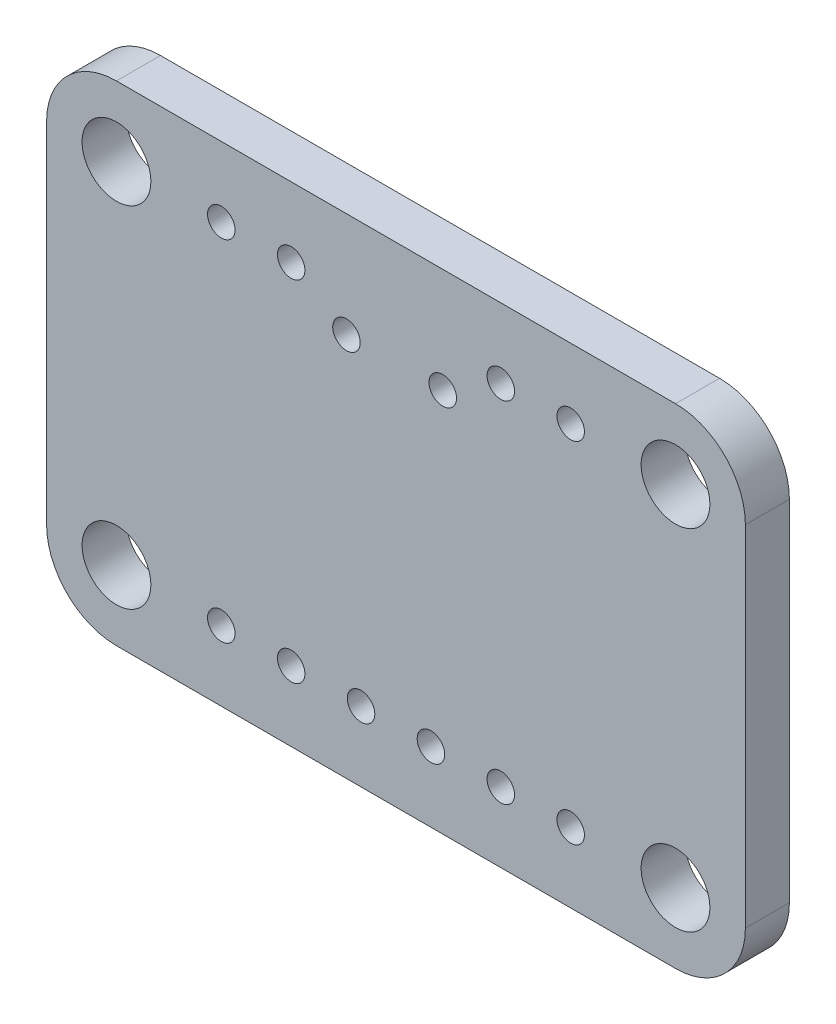
SolidWorks part; units mm, degrees
ref_plane "Front Plane" through (0, 0, 0) normal (0, 0, 1) x (1, 0, 0)
ref_plane "Top Plane" through (0, 0, 0) normal (0, 1, 0) x (1, 0, 0)
ref_plane "Right Plane" through (0, 0, 0) normal (1, 0, 0) x (0, 0, -1)
sketch "Model" plane through (0, 0, 0) normal (0, 0, 1) x (1, 0, 0)
  line L0 (0, 15.24) -> (0, 2.54)
  line L1 (2.54, 0) -> (22.86, 0)
  line L2 (25.4, 2.54) -> (25.4, 15.24)
  line L3 (22.86, 17.78) -> (2.54, 17.78)
  line L4 (15.6085, 7.087) -> (15.6085, 6.375)
  line L5 (14.7575, 7.087) -> (14.7575, 6.375)
  line L6 (15.5765, 6.731) -> (14.7765, 6.731)
  line L7 (7.1505, 9.652) -> (7.1505, 10.414)
  line L8 (8.4705, 9.677) -> (8.4705, 10.414)
  line L9 (7.3025, 10.033) -> (8.3185, 10.033)
  line L10 (8.2425, 6.7695) -> (8.2425, 6.0575)
  line L11 (7.3915, 6.7695) -> (7.3915, 6.0575)
  line L12 (8.2105, 6.4135) -> (7.4105, 6.4135)
  line L13 (24.819, 5.89) -> (20.569, 5.89)
  line L14 (20.569, 5.89) -> (20.569, 11.99)
  line L15 (20.569, 11.99) -> (24.819, 11.99)
  line L16 (24.819, 11.99) -> (24.819, 5.89)
  line L17 (23.119, 5.89) -> (20.519, 5.89)
  line L18 (20.519, 5.89) -> (20.519, 6.99)
  line L19 (20.519, 10.79) -> (20.519, 11.99)
  line L20 (20.519, 11.99) -> (23.119, 11.99)
  line L21 (24.819, 6.79) -> (24.819, 10.99)
  line L22 (0.6445, 11.89) -> (4.8945, 11.89)
  line L23 (4.8945, 11.89) -> (4.8945, 5.79)
  line L24 (4.8945, 5.79) -> (0.6445, 5.79)
  line L25 (0.6445, 5.79) -> (0.6445, 11.89)
  line L26 (2.3445, 11.89) -> (4.9445, 11.89)
  line L27 (4.9445, 11.89) -> (4.9445, 10.79)
  line L28 (4.9445, 6.99) -> (4.9445, 5.79)
  line L29 (4.9445, 5.79) -> (2.3445, 5.79)
  line L30 (0.6445, 10.99) -> (0.6445, 6.79)
  line L31 (3.6703, 12.5095) -> (3.9878, 12.2555)
  line L32 (3.9878, 12.2555) -> (3.9878, 12.7635)
  line L33 (3.9878, 12.7635) -> (3.6703, 12.5095)
  line L34 (3.8767, 12.3444) -> (3.9878, 12.3444)
  line L35 (3.6862, 12.4968) -> (3.9878, 12.4968)
  line L36 (3.8449, 12.6492) -> (3.9878, 12.6492)
  line L37 (3.435, 12.1095) -> (4.16, 12.1095)
  line L38 (3.46, 12.9095) -> (4.16, 12.9095)
  line L39 (13.084, 8.258) -> (13.084, 5.458)
  line L40 (13.084, 5.458) -> (10.284, 5.458)
  line L41 (10.284, 5.458) -> (10.284, 8.258)
  line L42 (10.284, 8.258) -> (13.084, 8.258)
  line L43 (11.184, 7.658) -> (10.584, 7.658)
  line L44 (5.08, 3.175) -> (5.08, 1.905)
  line L45 (15.24, 15.875) -> (15.24, 14.605)
  line L46 (5.08, 15.875) -> (5.08, 14.605)
  line L47 (17.0435, 7.671) -> (17.0435, 10.871)
  line L48 (17.0435, 10.871) -> (18.6435, 10.871)
  line L49 (18.6435, 10.871) -> (18.6435, 7.671)
  line L50 (18.6435, 7.671) -> (17.0435, 7.671)
  line L51 (16.4435, 11.171) -> (19.2435, 11.171)
  line L52 (19.2435, 7.371) -> (16.4435, 7.371)
  line L53 (6.274, 12.802) -> (6.274, 12.09)
  line L54 (5.423, 12.802) -> (5.423, 12.09)
  line L55 (6.242, 12.446) -> (5.442, 12.446)
  line L56 (17.6053, 13.335) -> (16.8116, 13.335)
  line L57 (17.2085, 13.7318) -> (17.2085, 12.9382)
  line L58 (8.4613, 13.3985) -> (7.6676, 13.3985)
  line L59 (16.1, 10.57) -> (16.1, 16.17)
  line L60 (16.1, 16.17) -> (16.1, 17.57)
  line L61 (16.1, 17.57) -> (9.1, 17.57)
  line L62 (9.1, 17.57) -> (9.1, 16.17)
  line L63 (9.1, 16.17) -> (9.1, 10.57)
  line L64 (9.1, 10.57) -> (16.1, 10.57)
  line L65 (16.1, 16.17) -> (9.1, 16.17)
  arc A0 (0, 2.54) -> (2.54, 0) centre (2.54, 2.54) ccw
  arc A1 (22.86, 0) -> (25.4, 2.54) centre (22.86, 2.54) ccw
  arc A2 (25.4, 15.24) -> (22.86, 17.78) centre (22.86, 15.24) ccw
  arc A3 (2.54, 17.78) -> (0, 15.24) centre (2.54, 15.24) ccw
  circle A4 centre (6.35, 2.54) radius 0.5
  circle A5 centre (8.89, 2.54) radius 0.5
  circle A6 centre (11.43, 2.54) radius 0.5
  circle A7 centre (13.97, 2.54) radius 0.5
  circle A8 centre (16.51, 2.54) radius 0.5
  circle A9 centre (19.05, 2.54) radius 0.5
  circle A10 centre (16.51, 15.24) radius 0.5
  circle A11 centre (19.05, 15.24) radius 0.5
  circle A12 centre (6.35, 15.24) radius 0.5
  circle A13 centre (8.89, 15.24) radius 0.5
  circle A14 centre (2.54, 15.24) radius 1.25
  circle A15 centre (22.86, 15.24) radius 1.25
  circle A16 centre (2.54, 2.54) radius 1.25
  circle A17 centre (22.86, 2.54) radius 1.25
  circle A18 centre (10.9, 13.97) radius 0.5
  circle A19 centre (14.4, 13.97) radius 0.5
  circle A20 centre (7.366, 4.318) radius 0.2413
  circle A21 centre (1.3335, 10.0965) radius 0.2413
  circle A22 centre (1.397, 7.4295) radius 0.2413
  circle A23 centre (24.13, 10.0965) radius 0.2413
  circle A24 centre (24.003, 7.5565) radius 0.2413
  circle A25 centre (9.398, 10.3505) radius 0.2413
  circle A26 centre (7.112, 13.2715) radius 0.2413
  circle A27 centre (16.002, 4.6355) radius 0.2413
  circle A28 centre (21.7805, 10.4775) radius 0.2413
  circle A29 centre (3.7465, 7.366) radius 0.2413
  circle A30 centre (12.5948, 6.0742) radius 0.2413
  circle A31 centre (21.8059, 9.1901) radius 0.2413
  circle A32 centre (3.7465, 6.2738) radius 0.2413
  circle A33 centre (11.5126, 6.3056) radius 0.2413
  circle A34 centre (22.606, 8.0645) radius 0.2413
  circle A35 centre (18.8595, 12.065) radius 0.2413
  circle A36 centre (3.2385, 10.795) radius 0.2413
  arc A37 (15.5831, 6.375) -> (15.6339, 6.375) centre (15.6085, 6.375) ccw
  arc A38 (15.6339, 7.087) -> (15.5831, 7.087) centre (15.6085, 7.087) ccw
  arc A39 (14.7321, 6.375) -> (14.7829, 6.375) centre (14.7575, 6.375) ccw
  arc A40 (14.7829, 7.087) -> (14.7321, 7.087) centre (14.7575, 7.087) ccw
  arc A41 (14.7765, 6.8072) -> (14.7765, 6.6548) centre (14.7765, 6.731) ccw
  arc A42 (15.5765, 6.6548) -> (15.5765, 6.8072) centre (15.5765, 6.731) ccw
  arc A43 (7.1759, 10.414) -> (7.1251, 10.414) centre (7.1505, 10.414) ccw
  arc A44 (7.1251, 9.652) -> (7.1759, 9.652) centre (7.1505, 9.652) ccw
  arc A45 (8.4959, 10.414) -> (8.4451, 10.414) centre (8.4705, 10.414) ccw
  arc A46 (8.4451, 9.677) -> (8.4959, 9.677) centre (8.4705, 9.677) ccw
  arc A47 (8.3185, 9.9568) -> (8.3185, 10.1092) centre (8.3185, 10.033) ccw
  arc A48 (7.3025, 10.1092) -> (7.3025, 9.9568) centre (7.3025, 10.033) ccw
  arc A49 (8.2171, 6.0575) -> (8.2679, 6.0575) centre (8.2425, 6.0575) ccw
  arc A50 (8.2679, 6.7695) -> (8.2171, 6.7695) centre (8.2425, 6.7695) ccw
  arc A51 (7.3661, 6.0575) -> (7.4169, 6.0575) centre (7.3915, 6.0575) ccw
  arc A52 (7.4169, 6.7695) -> (7.3661, 6.7695) centre (7.3915, 6.7695) ccw
  arc A53 (7.4105, 6.4897) -> (7.4105, 6.3373) centre (7.4105, 6.4135) ccw
  arc A54 (8.2105, 6.3373) -> (8.2105, 6.4897) centre (8.2105, 6.4135) ccw
  arc A55 (20.569, 5.9281) -> (20.569, 5.8519) centre (20.569, 5.89) ccw
  arc A56 (24.819, 5.8519) -> (24.819, 5.9281) centre (24.819, 5.89) ccw
  arc A57 (20.6071, 11.99) -> (20.5309, 11.99) centre (20.569, 11.99) ccw
  arc A58 (20.5309, 5.89) -> (20.6071, 5.89) centre (20.569, 5.89) ccw
  arc A59 (24.819, 11.9519) -> (24.819, 12.0281) centre (24.819, 11.99) ccw
  arc A60 (20.569, 12.0281) -> (20.569, 11.9519) centre (20.569, 11.99) ccw
  arc A61 (24.7809, 5.89) -> (24.8571, 5.89) centre (24.819, 5.89) ccw
  arc A62 (24.8571, 11.99) -> (24.7809, 11.99) centre (24.819, 11.99) ccw
  arc A63 (20.519, 5.9281) -> (20.519, 5.8519) centre (20.519, 5.89) ccw
  arc A64 (23.119, 5.8519) -> (23.119, 5.9281) centre (23.119, 5.89) ccw
  arc A65 (20.5571, 6.99) -> (20.4809, 6.99) centre (20.519, 6.99) ccw
  arc A66 (20.4809, 5.89) -> (20.5571, 5.89) centre (20.519, 5.89) ccw
  arc A67 (20.5571, 11.99) -> (20.4809, 11.99) centre (20.519, 11.99) ccw
  arc A68 (20.4809, 10.79) -> (20.5571, 10.79) centre (20.519, 10.79) ccw
  arc A69 (23.119, 11.9519) -> (23.119, 12.0281) centre (23.119, 11.99) ccw
  arc A70 (20.519, 12.0281) -> (20.519, 11.9519) centre (20.519, 11.99) ccw
  arc A71 (24.8571, 10.99) -> (24.7809, 10.99) centre (24.819, 10.99) ccw
  arc A72 (24.7809, 6.79) -> (24.8571, 6.79) centre (24.819, 6.79) ccw
  arc A73 (4.8945, 11.8519) -> (4.8945, 11.9281) centre (4.8945, 11.89) ccw
  arc A74 (0.6445, 11.9281) -> (0.6445, 11.8519) centre (0.6445, 11.89) ccw
  arc A75 (4.8564, 5.79) -> (4.9326, 5.79) centre (4.8945, 5.79) ccw
  arc A76 (4.9326, 11.89) -> (4.8564, 11.89) centre (4.8945, 11.89) ccw
  arc A77 (0.6445, 5.8281) -> (0.6445, 5.7519) centre (0.6445, 5.79) ccw
  arc A78 (4.8945, 5.7519) -> (4.8945, 5.8281) centre (4.8945, 5.79) ccw
  arc A79 (0.6826, 11.89) -> (0.6064, 11.89) centre (0.6445, 11.89) ccw
  arc A80 (0.6064, 5.79) -> (0.6826, 5.79) centre (0.6445, 5.79) ccw
  arc A81 (4.9445, 11.8519) -> (4.9445, 11.9281) centre (4.9445, 11.89) ccw
  arc A82 (2.3445, 11.9281) -> (2.3445, 11.8519) centre (2.3445, 11.89) ccw
  arc A83 (4.9064, 10.79) -> (4.9826, 10.79) centre (4.9445, 10.79) ccw
  arc A84 (4.9826, 11.89) -> (4.9064, 11.89) centre (4.9445, 11.89) ccw
  arc A85 (4.9064, 5.79) -> (4.9826, 5.79) centre (4.9445, 5.79) ccw
  arc A86 (4.9826, 6.99) -> (4.9064, 6.99) centre (4.9445, 6.99) ccw
  arc A87 (2.3445, 5.8281) -> (2.3445, 5.7519) centre (2.3445, 5.79) ccw
  arc A88 (4.9445, 5.7519) -> (4.9445, 5.8281) centre (4.9445, 5.79) ccw
  arc A89 (0.6064, 6.79) -> (0.6826, 6.79) centre (0.6445, 6.79) ccw
  arc A90 (0.6826, 10.99) -> (0.6064, 10.99) centre (0.6445, 10.99) ccw
  arc A91 (3.964, 12.2257) -> (4.0116, 12.2853) centre (3.9878, 12.2555) ccw
  arc A92 (3.6941, 12.5393) -> (3.6465, 12.4797) centre (3.6703, 12.5095) ccw
  arc A93 (4.0259, 12.7635) -> (3.9497, 12.7635) centre (3.9878, 12.7635) ccw
  arc A94 (3.9497, 12.2555) -> (4.0259, 12.2555) centre (3.9878, 12.2555) ccw
  arc A95 (3.6465, 12.5393) -> (3.6941, 12.4797) centre (3.6703, 12.5095) ccw
  arc A96 (4.0116, 12.7337) -> (3.964, 12.7933) centre (3.9878, 12.7635) ccw
  arc A97 (3.9878, 12.3063) -> (3.9878, 12.3825) centre (3.9878, 12.3444) ccw
  arc A98 (3.8767, 12.3825) -> (3.8767, 12.3063) centre (3.8767, 12.3444) ccw
  arc A99 (3.9878, 12.4587) -> (3.9878, 12.5349) centre (3.9878, 12.4968) ccw
  arc A100 (3.6862, 12.5349) -> (3.6862, 12.4587) centre (3.6862, 12.4968) ccw
  arc A101 (3.9878, 12.6111) -> (3.9878, 12.6873) centre (3.9878, 12.6492) ccw
  arc A102 (3.8449, 12.6873) -> (3.8449, 12.6111) centre (3.8449, 12.6492) ccw
  arc A103 (3.01, 12.2095) -> (3.01, 12.8095) centre (2.9839, 12.5095) ccw
  arc A104 (3.0078, 12.2348) -> (3.0122, 12.1842) centre (3.01, 12.2095) ccw
  arc A105 (3.0122, 12.8348) -> (3.0078, 12.7842) centre (3.01, 12.8095) ccw
  arc A106 (4.635, 12.7845) -> (4.635, 12.2345) centre (4.635, 12.5095) ccw
  arc A107 (4.635, 12.7718) -> (4.635, 12.7972) centre (4.635, 12.7845) ccw
  arc A108 (4.635, 12.2218) -> (4.635, 12.2472) centre (4.635, 12.2345) ccw
  arc A109 (4.16, 12.0841) -> (4.16, 12.1349) centre (4.16, 12.1095) ccw
  arc A110 (3.435, 12.1349) -> (3.435, 12.0841) centre (3.435, 12.1095) ccw
  arc A111 (4.16, 12.8841) -> (4.16, 12.9349) centre (4.16, 12.9095) ccw
  arc A112 (3.46, 12.9349) -> (3.46, 12.8841) centre (3.46, 12.9095) ccw
  circle A113 centre (3.185, 12.1595) radius 0.075
  arc A114 (13.0332, 5.458) -> (13.1348, 5.458) centre (13.084, 5.458) ccw
  arc A115 (13.1348, 8.258) -> (13.0332, 8.258) centre (13.084, 8.258) ccw
  arc A116 (10.284, 5.5088) -> (10.284, 5.4072) centre (10.284, 5.458) ccw
  arc A117 (13.084, 5.4072) -> (13.084, 5.5088) centre (13.084, 5.458) ccw
  arc A118 (10.3348, 8.258) -> (10.2332, 8.258) centre (10.284, 8.258) ccw
  arc A119 (10.2332, 5.458) -> (10.3348, 5.458) centre (10.284, 5.458) ccw
  arc A120 (13.084, 8.2072) -> (13.084, 8.3088) centre (13.084, 8.258) ccw
  arc A121 (10.284, 8.3088) -> (10.284, 8.2072) centre (10.284, 8.258) ccw
  arc A122 (11.184, 7.658) -> (10.584, 7.658) centre (10.884, 7.658) ccw
  arc A123 (11.1332, 7.658) -> (11.2348, 7.658) centre (11.184, 7.658) ccw
  arc A124 (10.5332, 7.658) -> (10.6348, 7.658) centre (10.584, 7.658) ccw
  arc A125 (10.584, 7.7088) -> (10.584, 7.6072) centre (10.584, 7.658) ccw
  arc A126 (11.184, 7.6072) -> (11.184, 7.7088) centre (11.184, 7.658) ccw
  arc A127 (5.0292, 1.905) -> (5.1308, 1.905) centre (5.08, 1.905) ccw
  arc A128 (5.1308, 3.175) -> (5.0292, 3.175) centre (5.08, 3.175) ccw
  arc A129 (15.1892, 14.605) -> (15.2908, 14.605) centre (15.24, 14.605) ccw
  arc A130 (15.2908, 15.875) -> (15.1892, 15.875) centre (15.24, 15.875) ccw
  arc A131 (5.0292, 14.605) -> (5.1308, 14.605) centre (5.08, 14.605) ccw
  arc A132 (5.1308, 15.875) -> (5.0292, 15.875) centre (5.08, 15.875) ccw
  arc A133 (17.0943, 10.871) -> (16.9927, 10.871) centre (17.0435, 10.871) ccw
  arc A134 (16.9927, 7.671) -> (17.0943, 7.671) centre (17.0435, 7.671) ccw
  arc A135 (18.6435, 10.8202) -> (18.6435, 10.9218) centre (18.6435, 10.871) ccw
  arc A136 (17.0435, 10.9218) -> (17.0435, 10.8202) centre (17.0435, 10.871) ccw
  arc A137 (18.5927, 7.671) -> (18.6943, 7.671) centre (18.6435, 7.671) ccw
  arc A138 (18.6943, 10.871) -> (18.5927, 10.871) centre (18.6435, 10.871) ccw
  arc A139 (17.0435, 7.7218) -> (17.0435, 7.6202) centre (17.0435, 7.671) ccw
  arc A140 (18.6435, 7.6202) -> (18.6435, 7.7218) centre (18.6435, 7.671) ccw
  arc A141 (19.2435, 11.1202) -> (19.2435, 11.2218) centre (19.2435, 11.171) ccw
  arc A142 (16.4435, 11.2218) -> (16.4435, 11.1202) centre (16.4435, 11.171) ccw
  arc A143 (16.4435, 7.4218) -> (16.4435, 7.3202) centre (16.4435, 7.371) ccw
  arc A144 (19.2435, 7.3202) -> (19.2435, 7.4218) centre (19.2435, 7.371) ccw
  arc A145 (6.2486, 12.09) -> (6.2994, 12.09) centre (6.274, 12.09) ccw
  arc A146 (6.2994, 12.802) -> (6.2486, 12.802) centre (6.274, 12.802) ccw
  arc A147 (5.3976, 12.09) -> (5.4484, 12.09) centre (5.423, 12.09) ccw
  arc A148 (5.4484, 12.802) -> (5.3976, 12.802) centre (5.423, 12.802) ccw
  arc A149 (5.442, 12.5222) -> (5.442, 12.3698) centre (5.442, 12.446) ccw
  arc A150 (6.242, 12.3698) -> (6.242, 12.5222) centre (6.242, 12.446) ccw
  arc A151 (16.8116, 13.4112) -> (16.8116, 13.2588) centre (16.8116, 13.335) ccw
  arc A152 (17.6053, 13.2588) -> (17.6053, 13.4112) centre (17.6053, 13.335) ccw
  arc A153 (17.1323, 12.9382) -> (17.2847, 12.9382) centre (17.2085, 12.9382) ccw
  arc A154 (17.2847, 13.7318) -> (17.1323, 13.7318) centre (17.2085, 13.7318) ccw
  circle A155 centre (17.2085, 13.335) radius 0.7817
  arc A156 (7.6676, 13.4747) -> (7.6676, 13.3223) centre (7.6676, 13.3985) ccw
  arc A157 (8.4613, 13.3223) -> (8.4613, 13.4747) centre (8.4613, 13.3985) ccw
  circle A158 centre (8.0645, 13.3985) radius 0.7817
  circle A159 centre (2.54, 15.24) radius 2
  circle A160 centre (22.86, 15.24) radius 2
  circle A161 centre (2.54, 2.54) radius 2
  circle A162 centre (22.86, 2.54) radius 2
  arc A163 (16.1508, 16.17) -> (16.0492, 16.17) centre (16.1, 16.17) ccw
  arc A164 (16.0492, 10.57) -> (16.1508, 10.57) centre (16.1, 10.57) ccw
  arc A165 (16.1508, 17.57) -> (16.0492, 17.57) centre (16.1, 17.57) ccw
  arc A166 (16.0492, 16.17) -> (16.1508, 16.17) centre (16.1, 16.17) ccw
  arc A167 (9.1, 17.6208) -> (9.1, 17.5192) centre (9.1, 17.57) ccw
  arc A168 (16.1, 17.5192) -> (16.1, 17.6208) centre (16.1, 17.57) ccw
  arc A169 (9.0492, 16.17) -> (9.1508, 16.17) centre (9.1, 16.17) ccw
  arc A170 (9.1508, 17.57) -> (9.0492, 17.57) centre (9.1, 17.57) ccw
  arc A171 (9.0492, 10.57) -> (9.1508, 10.57) centre (9.1, 10.57) ccw
  arc A172 (9.1508, 16.17) -> (9.0492, 16.17) centre (9.1, 16.17) ccw
  arc A173 (16.1, 10.5192) -> (16.1, 10.6208) centre (16.1, 10.57) ccw
  arc A174 (9.1, 10.6208) -> (9.1, 10.5192) centre (9.1, 10.57) ccw
  arc A175 (9.1, 16.2208) -> (9.1, 16.1192) centre (9.1, 16.17) ccw
  arc A176 (16.1, 16.1192) -> (16.1, 16.2208) centre (16.1, 16.17) ccw
extrude "Boss-Extrude1" add sketch "Model" against normal blind 1.6 contours A5 | A4 | L3 A3 L0 A0 L1 A1 L2 A2 | A9 | A8 | A7 | A6 | A11 | A10 | A13 | A12 | A17 | A16 | A19 | A18 | A15 | A14
sketch "Sketch3" plane through (0, 0, 0) normal (0, 0, 1) x (1, 0, 0)
  line L0 (0, 15.24) -> (0, 2.54)
  line L1 (2.54, 0) -> (22.86, 0)
  line L2 (25.4, 2.54) -> (25.4, 15.24)
  line L3 (22.86, 17.78) -> (2.54, 17.78)
  line L4 (15.6085, 7.087) -> (15.6085, 6.375)
  line L5 (14.7575, 7.087) -> (14.7575, 6.375)
  line L6 (15.5765, 6.731) -> (14.7765, 6.731)
  line L7 (7.1505, 9.652) -> (7.1505, 10.414)
  line L8 (8.4705, 9.677) -> (8.4705, 10.414)
  line L9 (7.3025, 10.033) -> (8.3185, 10.033)
  line L10 (8.2425, 6.7695) -> (8.2425, 6.0575)
  line L11 (7.3915, 6.7695) -> (7.3915, 6.0575)
  line L12 (8.2105, 6.4135) -> (7.4105, 6.4135)
  line L13 (24.819, 5.89) -> (20.569, 5.89)
  line L14 (20.569, 5.89) -> (20.569, 11.99)
  line L15 (20.569, 11.99) -> (24.819, 11.99)
  line L16 (24.819, 11.99) -> (24.819, 5.89)
  line L17 (23.119, 5.89) -> (20.519, 5.89)
  line L18 (20.519, 5.89) -> (20.519, 6.99)
  line L19 (20.519, 10.79) -> (20.519, 11.99)
  line L20 (20.519, 11.99) -> (23.119, 11.99)
  line L21 (24.819, 6.79) -> (24.819, 10.99)
  line L22 (0.6445, 11.89) -> (4.8945, 11.89)
  line L23 (4.8945, 11.89) -> (4.8945, 5.79)
  line L24 (4.8945, 5.79) -> (0.6445, 5.79)
  line L25 (0.6445, 5.79) -> (0.6445, 11.89)
  line L26 (2.3445, 11.89) -> (4.9445, 11.89)
  line L27 (4.9445, 11.89) -> (4.9445, 10.79)
  line L28 (4.9445, 6.99) -> (4.9445, 5.79)
  line L29 (4.9445, 5.79) -> (2.3445, 5.79)
  line L30 (0.6445, 10.99) -> (0.6445, 6.79)
  line L31 (3.6703, 12.5095) -> (3.9878, 12.2555)
  line L32 (3.9878, 12.2555) -> (3.9878, 12.7635)
  line L33 (3.9878, 12.7635) -> (3.6703, 12.5095)
  line L34 (3.8767, 12.3444) -> (3.9878, 12.3444)
  line L35 (3.6862, 12.4968) -> (3.9878, 12.4968)
  line L36 (3.8449, 12.6492) -> (3.9878, 12.6492)
  line L37 (3.435, 12.1095) -> (4.16, 12.1095)
  line L38 (3.46, 12.9095) -> (4.16, 12.9095)
  line L39 (13.084, 8.258) -> (13.084, 5.458)
  line L40 (13.084, 5.458) -> (10.284, 5.458)
  line L41 (10.284, 5.458) -> (10.284, 8.258)
  line L42 (10.284, 8.258) -> (13.084, 8.258)
  line L43 (11.184, 7.658) -> (10.584, 7.658)
  line L44 (5.08, 3.175) -> (5.08, 1.905)
  line L45 (15.24, 15.875) -> (15.24, 14.605)
  line L46 (5.08, 15.875) -> (5.08, 14.605)
  line L47 (17.0435, 7.671) -> (17.0435, 10.871)
  line L48 (17.0435, 10.871) -> (18.6435, 10.871)
  line L49 (18.6435, 10.871) -> (18.6435, 7.671)
  line L50 (18.6435, 7.671) -> (17.0435, 7.671)
  line L51 (16.4435, 11.171) -> (19.2435, 11.171)
  line L52 (19.2435, 7.371) -> (16.4435, 7.371)
  line L53 (6.274, 12.802) -> (6.274, 12.09)
  line L54 (5.423, 12.802) -> (5.423, 12.09)
  line L55 (6.242, 12.446) -> (5.442, 12.446)
  line L56 (17.6053, 13.335) -> (16.8116, 13.335)
  line L57 (17.2085, 13.7318) -> (17.2085, 12.9382)
  line L58 (8.4613, 13.3985) -> (7.6676, 13.3985)
  line L59 (16.1, 10.57) -> (16.1, 16.17)
  line L60 (16.1, 16.17) -> (16.1, 17.57)
  line L61 (16.1, 17.57) -> (9.1, 17.57)
  line L62 (9.1, 17.57) -> (9.1, 16.17)
  line L63 (9.1, 16.17) -> (9.1, 10.57)
  line L64 (9.1, 10.57) -> (16.1, 10.57)
  line L65 (16.1, 16.17) -> (9.1, 16.17)
  arc A0 (0, 2.54) -> (2.54, 0) centre (2.54, 2.54) ccw
  arc A1 (22.86, 0) -> (25.4, 2.54) centre (22.86, 2.54) ccw
  arc A2 (25.4, 15.24) -> (22.86, 17.78) centre (22.86, 15.24) ccw
  arc A3 (2.54, 17.78) -> (0, 15.24) centre (2.54, 15.24) ccw
  circle A4 centre (6.35, 2.54) radius 0.5
  circle A5 centre (8.89, 2.54) radius 0.5
  circle A6 centre (11.43, 2.54) radius 0.5
  circle A7 centre (13.97, 2.54) radius 0.5
  circle A8 centre (16.51, 2.54) radius 0.5
  circle A9 centre (19.05, 2.54) radius 0.5
  circle A10 centre (16.51, 15.24) radius 0.5
  circle A11 centre (19.05, 15.24) radius 0.5
  circle A12 centre (6.35, 15.24) radius 0.5
  circle A13 centre (8.89, 15.24) radius 0.5
  circle A14 centre (2.54, 15.24) radius 1.25
  circle A15 centre (22.86, 15.24) radius 1.25
  circle A16 centre (2.54, 2.54) radius 1.25
  circle A17 centre (22.86, 2.54) radius 1.25
  circle A18 centre (10.9, 13.97) radius 0.5
  circle A19 centre (14.4, 13.97) radius 0.5
  circle A20 centre (7.366, 4.318) radius 0.2413
  circle A21 centre (1.3335, 10.0965) radius 0.2413
  circle A22 centre (1.397, 7.4295) radius 0.2413
  circle A23 centre (24.13, 10.0965) radius 0.2413
  circle A24 centre (24.003, 7.5565) radius 0.2413
  circle A25 centre (9.398, 10.3505) radius 0.2413
  circle A26 centre (7.112, 13.2715) radius 0.2413
  circle A27 centre (16.002, 4.6355) radius 0.2413
  circle A28 centre (21.7805, 10.4775) radius 0.2413
  circle A29 centre (3.7465, 7.366) radius 0.2413
  circle A30 centre (12.5948, 6.0742) radius 0.2413
  circle A31 centre (21.8059, 9.1901) radius 0.2413
  circle A32 centre (3.7465, 6.2738) radius 0.2413
  circle A33 centre (11.5126, 6.3056) radius 0.2413
  circle A34 centre (22.606, 8.0645) radius 0.2413
  circle A35 centre (18.8595, 12.065) radius 0.2413
  circle A36 centre (3.2385, 10.795) radius 0.2413
  arc A37 (15.5831, 6.375) -> (15.6339, 6.375) centre (15.6085, 6.375) ccw
  arc A38 (15.6339, 7.087) -> (15.5831, 7.087) centre (15.6085, 7.087) ccw
  arc A39 (14.7321, 6.375) -> (14.7829, 6.375) centre (14.7575, 6.375) ccw
  arc A40 (14.7829, 7.087) -> (14.7321, 7.087) centre (14.7575, 7.087) ccw
  arc A41 (14.7765, 6.8072) -> (14.7765, 6.6548) centre (14.7765, 6.731) ccw
  arc A42 (15.5765, 6.6548) -> (15.5765, 6.8072) centre (15.5765, 6.731) ccw
  arc A43 (7.1759, 10.414) -> (7.1251, 10.414) centre (7.1505, 10.414) ccw
  arc A44 (7.1251, 9.652) -> (7.1759, 9.652) centre (7.1505, 9.652) ccw
  arc A45 (8.4959, 10.414) -> (8.4451, 10.414) centre (8.4705, 10.414) ccw
  arc A46 (8.4451, 9.677) -> (8.4959, 9.677) centre (8.4705, 9.677) ccw
  arc A47 (8.3185, 9.9568) -> (8.3185, 10.1092) centre (8.3185, 10.033) ccw
  arc A48 (7.3025, 10.1092) -> (7.3025, 9.9568) centre (7.3025, 10.033) ccw
  arc A49 (8.2171, 6.0575) -> (8.2679, 6.0575) centre (8.2425, 6.0575) ccw
  arc A50 (8.2679, 6.7695) -> (8.2171, 6.7695) centre (8.2425, 6.7695) ccw
  arc A51 (7.3661, 6.0575) -> (7.4169, 6.0575) centre (7.3915, 6.0575) ccw
  arc A52 (7.4169, 6.7695) -> (7.3661, 6.7695) centre (7.3915, 6.7695) ccw
  arc A53 (7.4105, 6.4897) -> (7.4105, 6.3373) centre (7.4105, 6.4135) ccw
  arc A54 (8.2105, 6.3373) -> (8.2105, 6.4897) centre (8.2105, 6.4135) ccw
  arc A55 (20.569, 5.9281) -> (20.569, 5.8519) centre (20.569, 5.89) ccw
  arc A56 (24.819, 5.8519) -> (24.819, 5.9281) centre (24.819, 5.89) ccw
  arc A57 (20.6071, 11.99) -> (20.5309, 11.99) centre (20.569, 11.99) ccw
  arc A58 (20.5309, 5.89) -> (20.6071, 5.89) centre (20.569, 5.89) ccw
  arc A59 (24.819, 11.9519) -> (24.819, 12.0281) centre (24.819, 11.99) ccw
  arc A60 (20.569, 12.0281) -> (20.569, 11.9519) centre (20.569, 11.99) ccw
  arc A61 (24.7809, 5.89) -> (24.8571, 5.89) centre (24.819, 5.89) ccw
  arc A62 (24.8571, 11.99) -> (24.7809, 11.99) centre (24.819, 11.99) ccw
  arc A63 (20.519, 5.9281) -> (20.519, 5.8519) centre (20.519, 5.89) ccw
  arc A64 (23.119, 5.8519) -> (23.119, 5.9281) centre (23.119, 5.89) ccw
  arc A65 (20.5571, 6.99) -> (20.4809, 6.99) centre (20.519, 6.99) ccw
  arc A66 (20.4809, 5.89) -> (20.5571, 5.89) centre (20.519, 5.89) ccw
  arc A67 (20.5571, 11.99) -> (20.4809, 11.99) centre (20.519, 11.99) ccw
  arc A68 (20.4809, 10.79) -> (20.5571, 10.79) centre (20.519, 10.79) ccw
  arc A69 (23.119, 11.9519) -> (23.119, 12.0281) centre (23.119, 11.99) ccw
  arc A70 (20.519, 12.0281) -> (20.519, 11.9519) centre (20.519, 11.99) ccw
  arc A71 (24.8571, 10.99) -> (24.7809, 10.99) centre (24.819, 10.99) ccw
  arc A72 (24.7809, 6.79) -> (24.8571, 6.79) centre (24.819, 6.79) ccw
  arc A73 (4.8945, 11.8519) -> (4.8945, 11.9281) centre (4.8945, 11.89) ccw
  arc A74 (0.6445, 11.9281) -> (0.6445, 11.8519) centre (0.6445, 11.89) ccw
  arc A75 (4.8564, 5.79) -> (4.9326, 5.79) centre (4.8945, 5.79) ccw
  arc A76 (4.9326, 11.89) -> (4.8564, 11.89) centre (4.8945, 11.89) ccw
  arc A77 (0.6445, 5.8281) -> (0.6445, 5.7519) centre (0.6445, 5.79) ccw
  arc A78 (4.8945, 5.7519) -> (4.8945, 5.8281) centre (4.8945, 5.79) ccw
  arc A79 (0.6826, 11.89) -> (0.6064, 11.89) centre (0.6445, 11.89) ccw
  arc A80 (0.6064, 5.79) -> (0.6826, 5.79) centre (0.6445, 5.79) ccw
  arc A81 (4.9445, 11.8519) -> (4.9445, 11.9281) centre (4.9445, 11.89) ccw
  arc A82 (2.3445, 11.9281) -> (2.3445, 11.8519) centre (2.3445, 11.89) ccw
  arc A83 (4.9064, 10.79) -> (4.9826, 10.79) centre (4.9445, 10.79) ccw
  arc A84 (4.9826, 11.89) -> (4.9064, 11.89) centre (4.9445, 11.89) ccw
  arc A85 (4.9064, 5.79) -> (4.9826, 5.79) centre (4.9445, 5.79) ccw
  arc A86 (4.9826, 6.99) -> (4.9064, 6.99) centre (4.9445, 6.99) ccw
  arc A87 (2.3445, 5.8281) -> (2.3445, 5.7519) centre (2.3445, 5.79) ccw
  arc A88 (4.9445, 5.7519) -> (4.9445, 5.8281) centre (4.9445, 5.79) ccw
  arc A89 (0.6064, 6.79) -> (0.6826, 6.79) centre (0.6445, 6.79) ccw
  arc A90 (0.6826, 10.99) -> (0.6064, 10.99) centre (0.6445, 10.99) ccw
  arc A91 (3.964, 12.2257) -> (4.0116, 12.2853) centre (3.9878, 12.2555) ccw
  arc A92 (3.6941, 12.5393) -> (3.6465, 12.4797) centre (3.6703, 12.5095) ccw
  arc A93 (4.0259, 12.7635) -> (3.9497, 12.7635) centre (3.9878, 12.7635) ccw
  arc A94 (3.9497, 12.2555) -> (4.0259, 12.2555) centre (3.9878, 12.2555) ccw
  arc A95 (3.6465, 12.5393) -> (3.6941, 12.4797) centre (3.6703, 12.5095) ccw
  arc A96 (4.0116, 12.7337) -> (3.964, 12.7933) centre (3.9878, 12.7635) ccw
  arc A97 (3.9878, 12.3063) -> (3.9878, 12.3825) centre (3.9878, 12.3444) ccw
  arc A98 (3.8767, 12.3825) -> (3.8767, 12.3063) centre (3.8767, 12.3444) ccw
  arc A99 (3.9878, 12.4587) -> (3.9878, 12.5349) centre (3.9878, 12.4968) ccw
  arc A100 (3.6862, 12.5349) -> (3.6862, 12.4587) centre (3.6862, 12.4968) ccw
  arc A101 (3.9878, 12.6111) -> (3.9878, 12.6873) centre (3.9878, 12.6492) ccw
  arc A102 (3.8449, 12.6873) -> (3.8449, 12.6111) centre (3.8449, 12.6492) ccw
  arc A103 (3.01, 12.2095) -> (3.01, 12.8095) centre (2.9839, 12.5095) ccw
  arc A104 (3.0078, 12.2348) -> (3.0122, 12.1842) centre (3.01, 12.2095) ccw
  arc A105 (3.0122, 12.8348) -> (3.0078, 12.7842) centre (3.01, 12.8095) ccw
  arc A106 (4.635, 12.7845) -> (4.635, 12.2345) centre (4.635, 12.5095) ccw
  arc A107 (4.635, 12.7718) -> (4.635, 12.7972) centre (4.635, 12.7845) ccw
  arc A108 (4.635, 12.2218) -> (4.635, 12.2472) centre (4.635, 12.2345) ccw
  arc A109 (4.16, 12.0841) -> (4.16, 12.1349) centre (4.16, 12.1095) ccw
  arc A110 (3.435, 12.1349) -> (3.435, 12.0841) centre (3.435, 12.1095) ccw
  arc A111 (4.16, 12.8841) -> (4.16, 12.9349) centre (4.16, 12.9095) ccw
  arc A112 (3.46, 12.9349) -> (3.46, 12.8841) centre (3.46, 12.9095) ccw
  circle A113 centre (3.185, 12.1595) radius 0.075
  arc A114 (13.0332, 5.458) -> (13.1348, 5.458) centre (13.084, 5.458) ccw
  arc A115 (13.1348, 8.258) -> (13.0332, 8.258) centre (13.084, 8.258) ccw
  arc A116 (10.284, 5.5088) -> (10.284, 5.4072) centre (10.284, 5.458) ccw
  arc A117 (13.084, 5.4072) -> (13.084, 5.5088) centre (13.084, 5.458) ccw
  arc A118 (10.3348, 8.258) -> (10.2332, 8.258) centre (10.284, 8.258) ccw
  arc A119 (10.2332, 5.458) -> (10.3348, 5.458) centre (10.284, 5.458) ccw
  arc A120 (13.084, 8.2072) -> (13.084, 8.3088) centre (13.084, 8.258) ccw
  arc A121 (10.284, 8.3088) -> (10.284, 8.2072) centre (10.284, 8.258) ccw
  arc A122 (11.184, 7.658) -> (10.584, 7.658) centre (10.884, 7.658) ccw
  arc A123 (11.1332, 7.658) -> (11.2348, 7.658) centre (11.184, 7.658) ccw
  arc A124 (10.5332, 7.658) -> (10.6348, 7.658) centre (10.584, 7.658) ccw
  arc A125 (10.584, 7.7088) -> (10.584, 7.6072) centre (10.584, 7.658) ccw
  arc A126 (11.184, 7.6072) -> (11.184, 7.7088) centre (11.184, 7.658) ccw
  arc A127 (5.0292, 1.905) -> (5.1308, 1.905) centre (5.08, 1.905) ccw
  arc A128 (5.1308, 3.175) -> (5.0292, 3.175) centre (5.08, 3.175) ccw
  arc A129 (15.1892, 14.605) -> (15.2908, 14.605) centre (15.24, 14.605) ccw
  arc A130 (15.2908, 15.875) -> (15.1892, 15.875) centre (15.24, 15.875) ccw
  arc A131 (5.0292, 14.605) -> (5.1308, 14.605) centre (5.08, 14.605) ccw
  arc A132 (5.1308, 15.875) -> (5.0292, 15.875) centre (5.08, 15.875) ccw
  arc A133 (17.0943, 10.871) -> (16.9927, 10.871) centre (17.0435, 10.871) ccw
  arc A134 (16.9927, 7.671) -> (17.0943, 7.671) centre (17.0435, 7.671) ccw
  arc A135 (18.6435, 10.8202) -> (18.6435, 10.9218) centre (18.6435, 10.871) ccw
  arc A136 (17.0435, 10.9218) -> (17.0435, 10.8202) centre (17.0435, 10.871) ccw
  arc A137 (18.5927, 7.671) -> (18.6943, 7.671) centre (18.6435, 7.671) ccw
  arc A138 (18.6943, 10.871) -> (18.5927, 10.871) centre (18.6435, 10.871) ccw
  arc A139 (17.0435, 7.7218) -> (17.0435, 7.6202) centre (17.0435, 7.671) ccw
  arc A140 (18.6435, 7.6202) -> (18.6435, 7.7218) centre (18.6435, 7.671) ccw
  arc A141 (19.2435, 11.1202) -> (19.2435, 11.2218) centre (19.2435, 11.171) ccw
  arc A142 (16.4435, 11.2218) -> (16.4435, 11.1202) centre (16.4435, 11.171) ccw
  arc A143 (16.4435, 7.4218) -> (16.4435, 7.3202) centre (16.4435, 7.371) ccw
  arc A144 (19.2435, 7.3202) -> (19.2435, 7.4218) centre (19.2435, 7.371) ccw
  arc A145 (6.2486, 12.09) -> (6.2994, 12.09) centre (6.274, 12.09) ccw
  arc A146 (6.2994, 12.802) -> (6.2486, 12.802) centre (6.274, 12.802) ccw
  arc A147 (5.3976, 12.09) -> (5.4484, 12.09) centre (5.423, 12.09) ccw
  arc A148 (5.4484, 12.802) -> (5.3976, 12.802) centre (5.423, 12.802) ccw
  arc A149 (5.442, 12.5222) -> (5.442, 12.3698) centre (5.442, 12.446) ccw
  arc A150 (6.242, 12.3698) -> (6.242, 12.5222) centre (6.242, 12.446) ccw
  arc A151 (16.8116, 13.4112) -> (16.8116, 13.2588) centre (16.8116, 13.335) ccw
  arc A152 (17.6053, 13.2588) -> (17.6053, 13.4112) centre (17.6053, 13.335) ccw
  arc A153 (17.1323, 12.9382) -> (17.2847, 12.9382) centre (17.2085, 12.9382) ccw
  arc A154 (17.2847, 13.7318) -> (17.1323, 13.7318) centre (17.2085, 13.7318) ccw
  circle A155 centre (17.2085, 13.335) radius 0.7817
  arc A156 (7.6676, 13.4747) -> (7.6676, 13.3223) centre (7.6676, 13.3985) ccw
  arc A157 (8.4613, 13.3223) -> (8.4613, 13.4747) centre (8.4613, 13.3985) ccw
  circle A158 centre (8.0645, 13.3985) radius 0.7817
  circle A159 centre (2.54, 15.24) radius 2
  circle A160 centre (22.86, 15.24) radius 2
  circle A161 centre (2.54, 2.54) radius 2
  circle A162 centre (22.86, 2.54) radius 2
  arc A163 (16.1508, 16.17) -> (16.0492, 16.17) centre (16.1, 16.17) ccw
  arc A164 (16.0492, 10.57) -> (16.1508, 10.57) centre (16.1, 10.57) ccw
  arc A165 (16.1508, 17.57) -> (16.0492, 17.57) centre (16.1, 17.57) ccw
  arc A166 (16.0492, 16.17) -> (16.1508, 16.17) centre (16.1, 16.17) ccw
  arc A167 (9.1, 17.6208) -> (9.1, 17.5192) centre (9.1, 17.57) ccw
  arc A168 (16.1, 17.5192) -> (16.1, 17.6208) centre (16.1, 17.57) ccw
  arc A169 (9.0492, 16.17) -> (9.1508, 16.17) centre (9.1, 16.17) ccw
  arc A170 (9.1508, 17.57) -> (9.0492, 17.57) centre (9.1, 17.57) ccw
  arc A171 (9.0492, 10.57) -> (9.1508, 10.57) centre (9.1, 10.57) ccw
  arc A172 (9.1508, 16.17) -> (9.0492, 16.17) centre (9.1, 16.17) ccw
  arc A173 (16.1, 10.5192) -> (16.1, 10.6208) centre (16.1, 10.57) ccw
  arc A174 (9.1, 10.6208) -> (9.1, 10.5192) centre (9.1, 10.57) ccw
  arc A175 (9.1, 16.2208) -> (9.1, 16.1192) centre (9.1, 16.17) ccw
  arc A176 (16.1, 16.1192) -> (16.1, 16.2208) centre (16.1, 16.17) ccw
